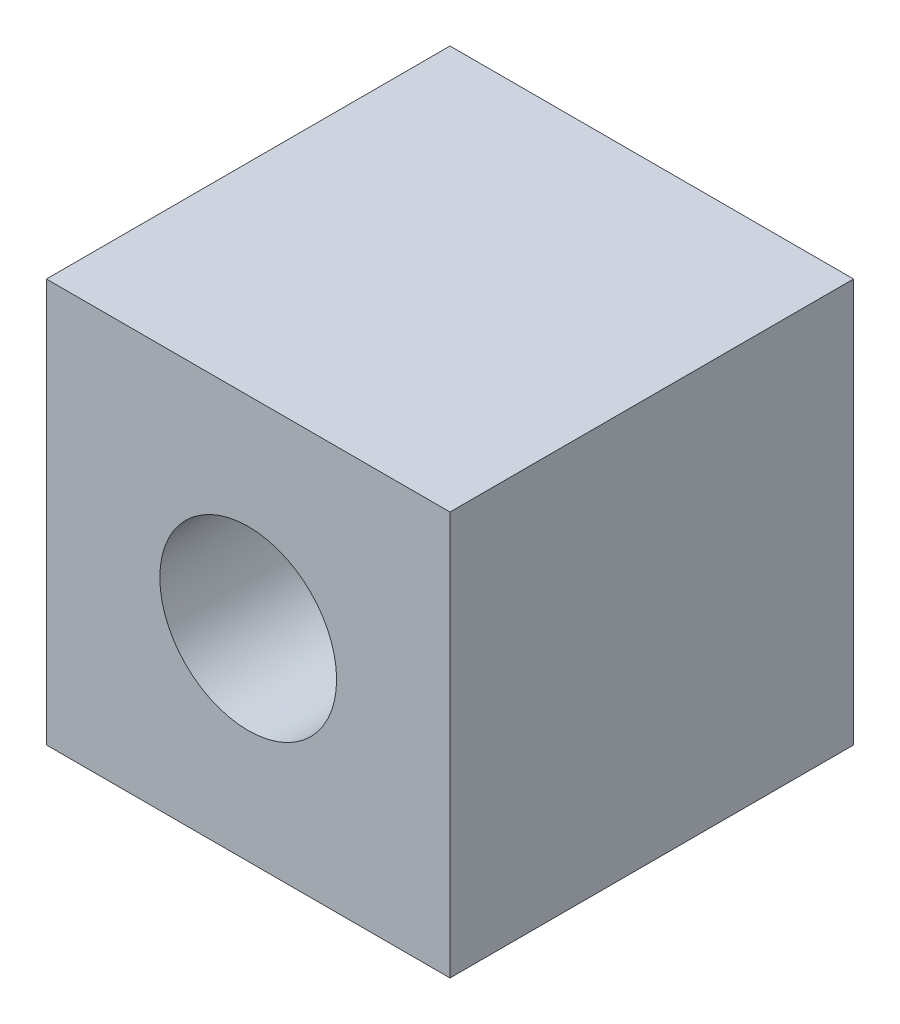
SolidWorks part; units mm, degrees
ref_plane "Front Plane" through (0, 0, 0) normal (0, 0, 1) x (1, 0, 0)
ref_plane "Top Plane" through (0, 0, 0) normal (0, 1, 0) x (1, 0, 0)
ref_plane "Right Plane" through (0, 0, 0) normal (1, 0, 0) x (0, 0, -1)
sketch "Sketch1" plane through (0, 0, 0) normal (0, 1, 0) x (1, 0, 0)
  line L1 (-12.7, -12.7) -> (12.7, -12.7)
  line L2 (-12.7, -12.7) -> (-12.7, 12.7)
  line L3 (-12.7, 12.7) -> (12.7, 12.7)
  line L4 (12.7, -12.7) -> (12.7, 12.7)
  line L5 (-12.7, -12.7) -> (12.7, 12.7) construction
  line L6 (-12.7, 12.7) -> (12.7, -12.7) construction
  point P0 (0, 0)
  dimension "D1" = 25.4
  dimension "D2" = 25.4
extrude "Boss-Extrude1" add sketch "Sketch1" along normal blind 25.4 contours L1 L4 L3 L2
sketch "Sketch2" plane through (0, 0, 12.7) normal (0, 0, 1) x (1, 0, 0)
  line L0 (0, 12.7) -> (0, 25.4) construction
  line L1 (-12.7, 25.4) -> (12.7, 25.4) construction
  line L2 (0, 12.7) -> (0, 0) construction
  line L3 (-12.7, 0) -> (12.7, 0) construction
  circle A0 centre (0, 12.7) radius 5.5626
  dimension "D1" = 11.1252
extrude "Cut-Extrude1" cut sketch "Sketch2" against normal blind 76.2
equation "\"D2@Sketch1\"=\"D1@Sketch1\""
equation "\"D1@Boss-Extrude1\"=\"D1@Sketch1\""
